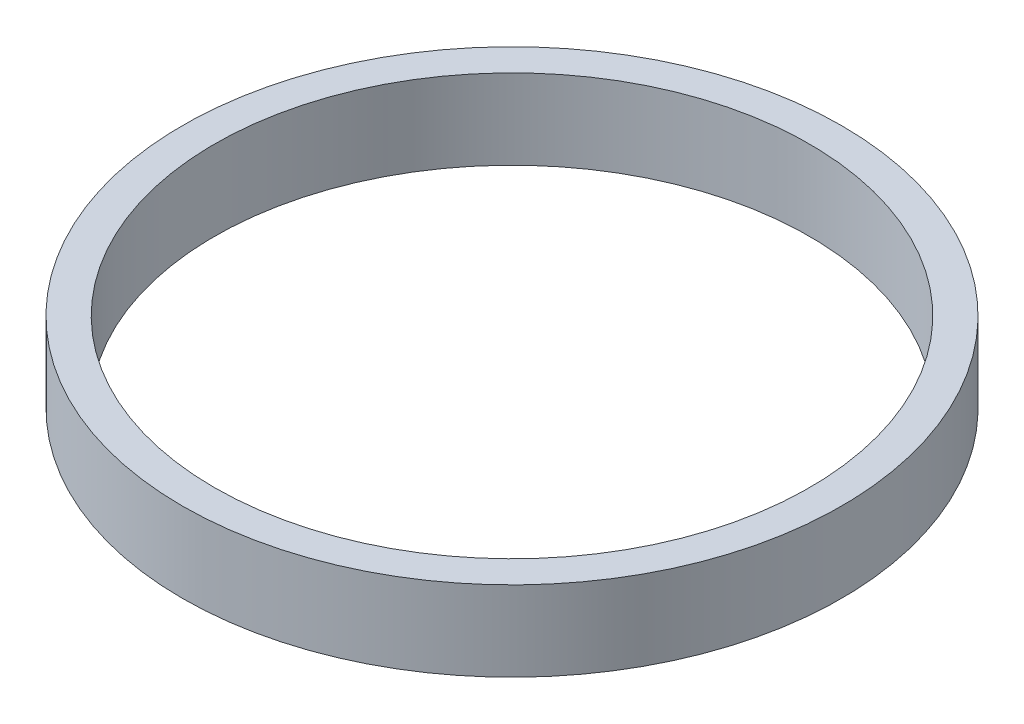
SolidWorks part; units mm, degrees
ref_plane "Plan de face" through (0, 0, 0) normal (0, 0, 1) x (1, 0, 0)
ref_plane "Plan de dessus" through (0, 0, 0) normal (0, 1, 0) x (1, 0, 0)
ref_plane "Plan de droite" through (0, 0, 0) normal (1, 0, 0) x (0, 0, -1)
sketch "Esquisse1" plane through (0, 0, 0) normal (0, 1, 0) x (1, 0, 0)
  circle A0 centre (0, 0) radius 18.6
  circle A1 centre (0, 0) radius 20.6
  dimension "D1" = 37.2
  dimension "D2" = 2
extrude "Boss.-Extru.1" add sketch "Esquisse1" along normal blind 5
